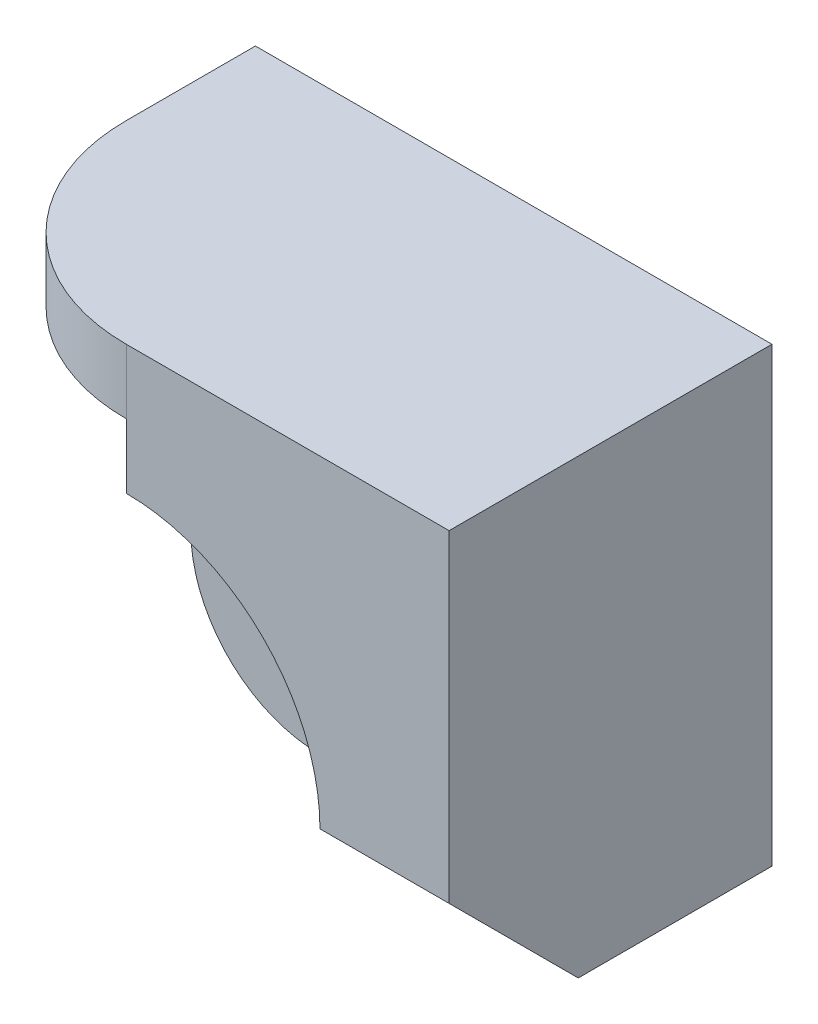
SolidWorks part; units mm, degrees
ref_plane "Front Plane" through (0, 0, 0) normal (0, 0, 1) x (1, 0, 0)
ref_plane "Top Plane" through (0, 0, 0) normal (0, 1, 0) x (1, 0, 0)
ref_plane "Right Plane" through (0, 0, 0) normal (1, 0, 0) x (0, 0, -1)
sketch "Sketch1" plane through (0, 0, 0) normal (0, 0, 1) x (1, 0, 0)
  line L0 (-2, 0) -> (-2, 4)
  line L1 (-2, 4) -> (-3, 4)
  line L2 (-3, 4) -> (-3, 5)
  line L3 (-3, 5) -> (5, 5)
  line L4 (5, 5) -> (5, -2)
  line L5 (5, -2) -> (0, -2)
  circle A0 centre (0, 0) radius 1
  arc A1 (-2, 0) -> (0, -2) centre (0, 0) ccw
  dimension "D1" = 2
  dimension "D2" = 2
  dimension "D3" = 4
  dimension "D4" = 1
  dimension "D5" = 5
  dimension "D6" = 7
  dimension "D7" = 1
extrude "Boss-Extrude1" add sketch "Sketch1" along normal blind 5
sketch "Sketch2" plane through (0, 0, 5) normal (0, 0, 1) x (1, 0, 0)
  line L0 (5, -2) -> (5, 5)
  line L1 (5, 5) -> (-3, 5)
  line L2 (-3, 5) -> (-3, 4)
  line L3 (-3, 4) -> (-2, 4)
  line L4 (-2, 4) -> (0, 4)
  line L5 (0, 4) -> (0, 3)
  line L6 (5, -2) -> (3, -2)
  line L7 (0, -2) -> (5, -2) construction
  line L8 (3, -2) -> (3, 0)
  arc A0 (0, 3) -> (3, 0) centre (0, 0) cw
  dimension "D1" = 2
  dimension "D2" = 2
  dimension "D3" = 2
  dimension "D4" = 1
extrude "Cut-Extrude1" cut sketch "Sketch2" against normal blind 3 flip side to cut
sketch "Sketch3" plane through (0, 4, 0) normal (0, -1, 0) x (1, 0, 0)
  line L0 (-3, 2) -> (-3, 5)
  line L1 (-3, 5) -> (0, 5)
  arc A0 (0, 5) -> (-3, 2) centre (0, 2) ccw
extrude "Cut-Extrude2" cut sketch "Sketch3" against normal blind 3
sketch "Sketch4" plane through (3, 0, 0) normal (-1, 0, 0) x (0, 0, 1)
  line L0 (5, 0) -> (3, -2)
  line L1 (2, -2) -> (5, -2) construction
  line L2 (3, -2) -> (5, -2)
  line L3 (5, -2) -> (5, 0)
  dimension "D1" = 1
extrude "Cut-Extrude3" cut sketch "Sketch4" against normal through all
